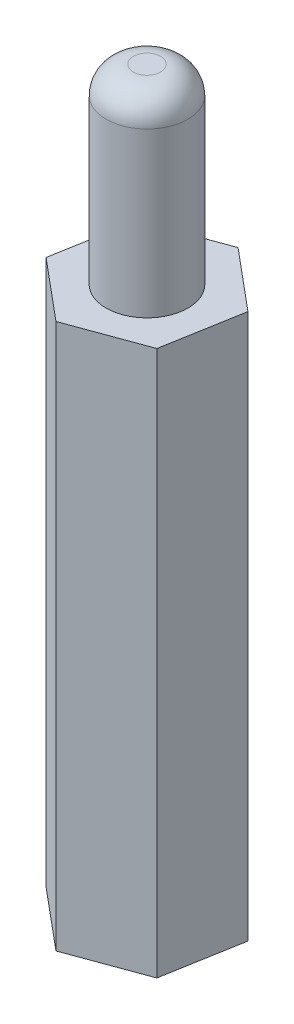
SolidWorks part; units mm, degrees
ref_plane "Front Plane" through (0, 0, 0) normal (0, 0, 1) x (1, 0, 0)
ref_plane "Top Plane" through (0, 0, 0) normal (0, 1, 0) x (1, 0, 0)
ref_plane "Right Plane" through (0, 0, 0) normal (1, 0, 0) x (0, 0, -1)
sketch "Sketch1" plane through (0, 0, 0) normal (0, 1, 0) x (1, 0, 0)
  line L1 (2.2148, -1.8515) -> (2.7108, 0.9924)
  line L2 (2.7108, 0.9924) -> (0.496, 2.8438)
  line L3 (0.496, 2.8438) -> (-2.2148, 1.8515)
  line L4 (-2.2148, 1.8515) -> (-2.7108, -0.9924)
  line L5 (-2.7108, -0.9924) -> (-0.496, -2.8438)
  line L6 (-0.496, -2.8438) -> (2.2148, -1.8515)
  circle A0 centre (0, 0) radius 2.5 construction
  dimension "D1" = 5
extrude "Boss-Extrude1" add sketch "Sketch1" along normal blind 20
sketch "Sketch2" plane through (0, 20, 0) normal (0, 1, 0) x (1, 0, 0)
  circle A0 centre (0, 0) radius 1.5
  dimension "D1" = 3
extrude "Boss-Extrude2" add sketch "Sketch2" along normal blind 7
sketch "Sketch3" plane through (0, 0, 0) normal (0, -1, 0) x (1, 0, 0)
  circle A0 centre (0, 0) radius 1.5
extrude "Cut-Extrude1" cut sketch "Sketch3" against normal blind 7
fillet "Fillet1" radius 1 1 edges at (0, 27, 1.5)
